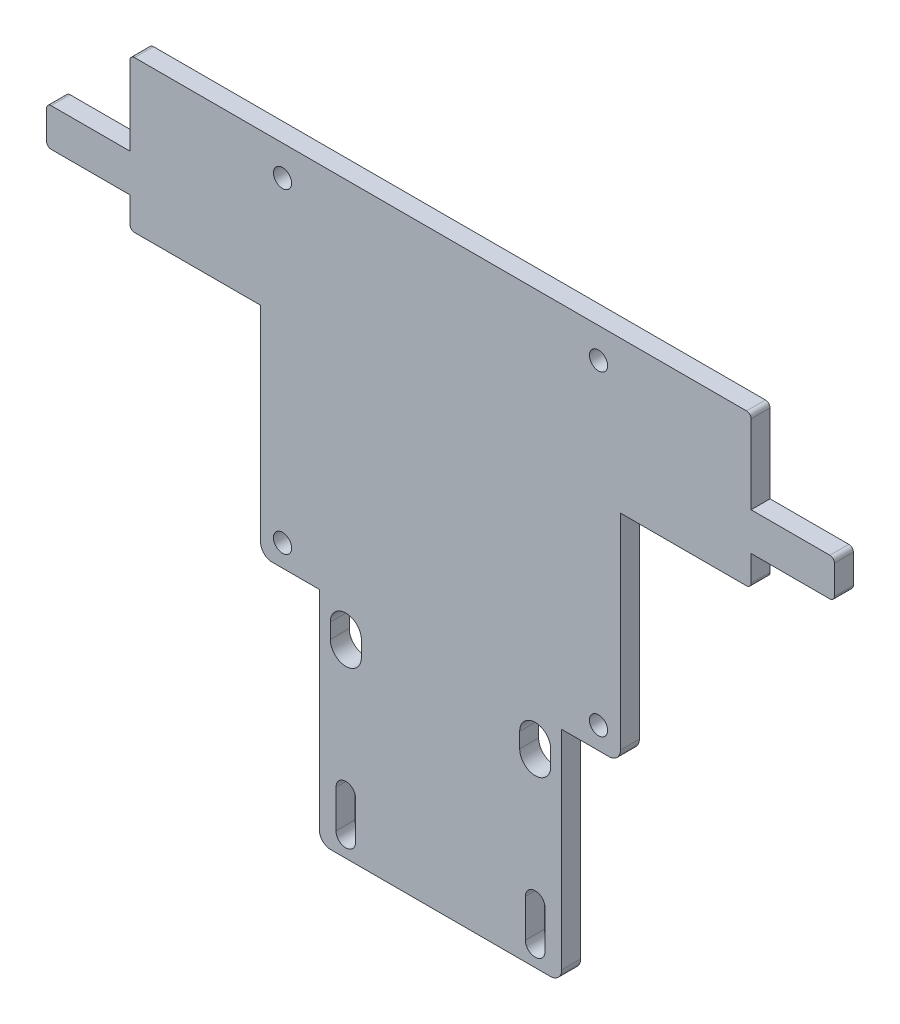
SolidWorks part; units mm, degrees
ref_plane "Front Plane" through (0, 0, 0) normal (0, 0, 1) x (1, 0, 0)
ref_plane "Top Plane" through (0, 0, 0) normal (0, 1, 0) x (1, 0, 0)
ref_plane "Right Plane" through (0, 0, 0) normal (1, 0, 0) x (0, 0, -1)
sketch "Sketch1" plane through (0, 0, 0) normal (0, 0, 1) x (1, 0, 0)
  line L0 (52.07, 25.4) -> (52.07, -6.1659) construction
  line L1 (0.762, 0) -> (21.9075, 0)
  line L2 (0, 0.762) -> (0, 5.08)
  line L3 (0.762, 25.4) -> (103.378, 25.4)
  line L4 (104.14, 0.762) -> (104.14, 5.08)
  line L5 (-13.208, 5.08) -> (0, 5.08)
  line L6 (-13.97, 5.842) -> (-13.97, 10.668)
  line L7 (-13.208, 11.43) -> (0, 11.43)
  line L8 (118.11, 5.842) -> (118.11, 10.668)
  line L9 (-13.97, 8.255) -> (118.11, 8.255) construction
  line L10 (0, 11.43) -> (0, 24.638)
  line L11 (104.14, 11.43) -> (117.348, 11.43)
  line L12 (104.14, 11.43) -> (104.14, 24.638)
  line L13 (104.14, 5.08) -> (117.348, 5.08)
  line L14 (21.9075, -6.1659) -> (82.2325, -6.1659) construction
  line L15 (36.195, -41.4084) -> (67.945, -41.4084) construction
  line L16 (23.8125, -36.3284) -> (31.75, -36.3284)
  line L17 (21.9075, -34.4233) -> (21.9075, 0)
  line L19 (82.2325, -34.4233) -> (82.2325, 0)
  line L20 (36.195, -40.1384) -> (36.195, -42.6784) construction
  line L21 (72.39, -36.3284) -> (80.3275, -36.3284)
  line L23 (31.75, -36.3284) -> (31.75, -71.2534)
  line L24 (33.655, -73.1584) -> (70.485, -73.1584)
  line L25 (72.39, -36.3284) -> (72.39, -71.2534)
  line L26 (38.7985, -40.1384) -> (38.7985, -42.6784)
  line L27 (33.5915, -40.1384) -> (33.5915, -42.6784)
  line L28 (67.945, -40.1384) -> (67.945, -42.6784) construction
  line L29 (82.2325, 0) -> (103.378, 0)
  line L30 (70.5485, -40.1384) -> (70.5485, -42.6784)
  line L31 (65.3415, -40.1384) -> (65.3415, -42.6784)
  line L32 (36.195, -66.8084) -> (67.945, -66.8084) construction
  line L33 (67.945, -63.6334) -> (67.945, -69.9834) construction
  line L34 (69.595, -63.6334) -> (69.595, -69.9834)
  line L35 (66.295, -63.6334) -> (66.295, -69.9834)
  line L36 (36.195, -63.6334) -> (36.195, -69.9834) construction
  line L37 (37.845, -63.6334) -> (37.845, -69.9834)
  line L38 (34.545, -63.6334) -> (34.545, -69.9834)
  arc A0 (103.378, 0) -> (104.14, 0.762) centre (103.378, 0.762) ccw
  arc A1 (0.762, 0) -> (0, 0.762) centre (0.762, 0.762) cw
  arc A2 (-13.208, 5.08) -> (-13.97, 5.842) centre (-13.208, 5.842) cw
  arc A3 (-13.97, 10.668) -> (-13.208, 11.43) centre (-13.208, 10.668) cw
  arc A4 (117.348, 5.08) -> (118.11, 5.842) centre (117.348, 5.842) ccw
  arc A5 (117.348, 11.43) -> (118.11, 10.668) centre (117.348, 10.668) cw
  arc A6 (103.378, 25.4) -> (104.14, 24.638) centre (103.378, 24.638) cw
  arc A7 (0, 24.638) -> (0.762, 25.4) centre (0.762, 24.638) cw
  circle A9 centre (25.5841, 20.32) radius 1.524
  circle A10 centre (78.5558, 20.32) radius 1.524
  circle A11 centre (78.5558, -32.6517) radius 1.524
  circle A12 centre (25.5841, -32.6517) radius 1.524
  arc A13 (80.3275, -36.3284) -> (82.2325, -34.4233) centre (80.3275, -34.4234) ccw
  arc A14 (23.8125, -36.3284) -> (21.9075, -34.4233) centre (23.8125, -34.4234) cw
  arc A15 (70.485, -73.1584) -> (72.39, -71.2534) centre (70.485, -71.2534) ccw
  arc A16 (31.75, -71.2534) -> (33.655, -73.1584) centre (33.655, -71.2534) ccw
  arc A17 (38.7985, -40.1384) -> (33.5915, -40.1384) centre (36.195, -40.1384) ccw
  arc A18 (33.5915, -42.6784) -> (38.7985, -42.6784) centre (36.195, -42.6784) ccw
  arc A19 (70.5485, -40.1384) -> (65.3415, -40.1384) centre (67.945, -40.1384) ccw
  arc A20 (65.3415, -42.6784) -> (70.5485, -42.6784) centre (67.945, -42.6784) ccw
  arc A21 (69.595, -63.6334) -> (66.295, -63.6334) centre (67.945, -63.6334) ccw
  arc A22 (66.295, -69.9834) -> (69.595, -69.9834) centre (67.945, -69.9834) ccw
  arc A23 (37.845, -63.6334) -> (34.545, -63.6334) centre (36.195, -63.6334) ccw
  arc A24 (34.545, -69.9834) -> (37.845, -69.9834) centre (36.195, -69.9834) ccw
  point P21 (0, 0)
  point P24 (-13.97, 5.08)
  point P27 (-13.97, 11.43)
  point P34 (104.14, 25.4)
  point P37 (0, 25.4)
  point P50 (52.07, -73.1584)
  point P59 (52.07, -41.4084)
  point P64 (36.195, -41.4084)
  point P76 (67.945, -41.4084)
  point P85 (52.07, -66.8084)
  point P87 (67.945, -66.8084)
  point P93 (36.195, -66.8084)
  dimension "D6" = 0.762
  dimension "D7" = 40.64
  dimension "D8" = 52.9717
  dimension "D10" = 3.048
  dimension "D13" = 1.905
  dimension "D18" = 1.905
  dimension "D19" = 2.6035
  dimension "D21" = 1.65
  dimension "D1" = 25.4
  dimension "D2" = 104.14
  dimension "D3" = 6.35
  dimension "D4" = 132.08
  dimension "D5" = 17.145
  dimension "D9" = 5.08
  dimension "D11" = 26.4859
  dimension "D12" = 31.75
  dimension "D14" = 5.08
  dimension "D15" = 31.75
  dimension "D16" = 60.325
  dimension "D17" = 30.1625
  dimension "D20" = 2.54
  dimension "D22" = 6.35
  dimension "D23" = 31.75
  dimension "D24" = 6.35
extrude "Boss-Extrude1" add sketch "Sketch1" along normal blind 3.175
